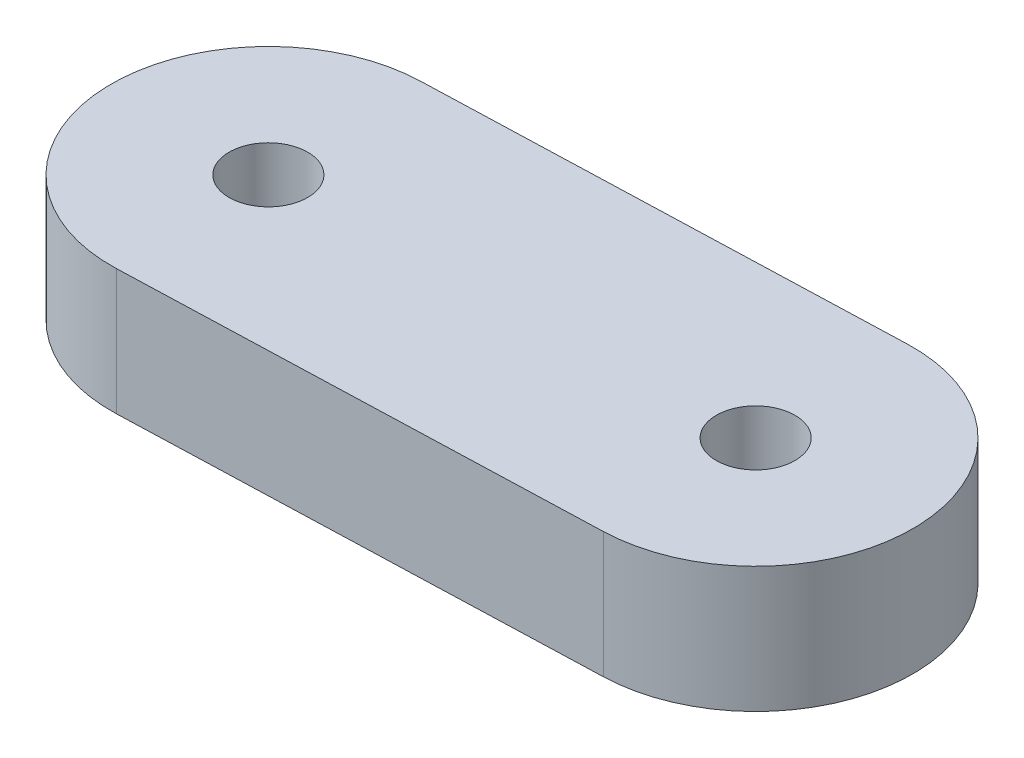
SolidWorks part; units mm, degrees
ref_plane "Front Plane" through (0, 0, 0) normal (0, 0, 1) x (1, 0, 0)
ref_plane "Top Plane" through (0, 0, 0) normal (0, 1, 0) x (1, 0, 0)
ref_plane "Right Plane" through (0, 0, 0) normal (1, 0, 0) x (0, 0, -1)
sketch "Sketch1" plane through (0, 0, 0) normal (0, 1, 0) x (1, 0, 0)
  line L0 (0, 0) -> (-299.832, -10.0385) construction
  line L1 (3.3462, -99.944) -> (-296.4858, -109.9825)
  line L2 (-3.3462, 99.944) -> (-303.1782, 89.9055)
  arc A0 (3.3462, -99.944) -> (-3.3462, 99.944) centre (0, 0) ccw
  arc A1 (-303.1782, 89.9055) -> (-296.4858, -109.9825) centre (-299.832, -10.0385) ccw
  point P3 (-149.916, -5.0192)
extrude "Boss-Extrude1" add sketch "Sketch1" along normal blind 80
sketch "Sketch2" plane through (0, 80, 0) normal (0, 1, 0) x (1, 0, 0)
  circle A0 centre (0, 0) radius 25
extrude "Cut-Extrude1" cut sketch "Sketch2" against normal blind 50
sketch "Sketch3" plane through (0, 80, 0) normal (0, 1, 0) x (1, 0, 0)
  circle A0 centre (-299.832, -10.0385) radius 25
extrude "Cut-Extrude2" cut sketch "Sketch3" against normal blind 80
